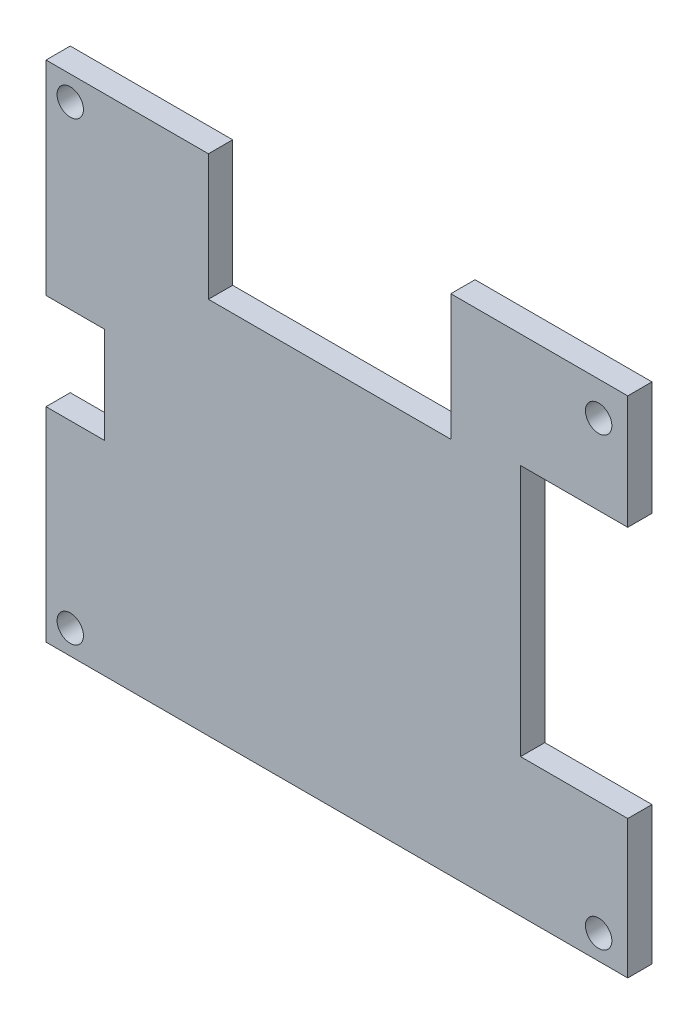
SolidWorks part; units mm, degrees
ref_plane "Front Plane" through (0, 0, 0) normal (0, 0, 1) x (1, 0, 0)
ref_plane "Top Plane" through (0, 0, 0) normal (0, 1, 0) x (1, 0, 0)
ref_plane "Right Plane" through (0, 0, 0) normal (1, 0, 0) x (0, 0, -1)
sketch "Sketch1" plane through (0, 0, 0) normal (0, 0, 1) x (1, 0, 0)
  line L0 (38.1, 1.5875) -> (24.0608, 1.5875) construction
  line L1 (-38.1, 33.02) -> (38.1, 33.02) construction
  line L2 (-38.1, 33.02) -> (-38.1, -33.02) construction
  line L3 (-38.1, -33.02) -> (38.1, -33.02) construction
  line L4 (38.1, 33.02) -> (38.1, -33.02) construction
  line L5 (-38.1, 33.02) -> (38.1, -33.02) construction
  line L6 (-38.1, -33.02) -> (38.1, 33.02) construction
  line L7 (-41.275, 6.3059) -> (-41.275, -6.3059)
  line L8 (-41.275, 6.3059) -> (-30.4454, 6.3059)
  line L9 (41.275, 18.1012) -> (41.275, -14.9262)
  line L10 (-41.275, -6.3059) -> (-30.4454, -6.3059)
  line L11 (-30.4454, 6.3059) -> (-30.4454, -6.3059)
  line L12 (41.275, 18.1012) -> (24.0608, 18.1012)
  line L13 (-34.925, 0) -> (-30.4454, 0) construction
  line L15 (41.275, -14.9262) -> (24.0608, -14.9262)
  line L16 (24.0608, 18.1012) -> (24.0608, -14.9262)
  line L18 (-16.8275, 16.51) -> (14.9225, 16.51)
  line L20 (-16.8275, 16.51) -> (-16.8275, 36.195)
  line L21 (-16.8275, 36.195) -> (14.9225, 36.195)
  line L22 (14.9225, 16.51) -> (14.9225, 36.195)
  point P0 (0, 0)
  point P6 (-34.925, 0)
  point P7 (33.655, 10.795)
  point P8 (-9.525, 20.32)
  point P9 (6.35, 24.13)
  point P10 (33.655, -7.62)
  point P11 (33.655, 1.5875)
  point P15 (33.655, 1.5875)
  point P29 (-16.8275, 16.51)
  point P30 (14.9225, 33.02)
  point P37 (-34.925, 29.845)
  point P38 (34.29, 28.575)
  point P40 (34.29, -29.845)
  point P42 (-34.925, -29.845)
  dimension "D1" = 76.2
  dimension "D2" = 66.04
  dimension "D3" = 3.175
  dimension "D4" = 33.02
  dimension "D5" = 28.575
  dimension "D6" = 53.34
  dimension "D7" = 57.15
  dimension "D8" = 44.45
  dimension "D9" = 71.755
  dimension "D10" = 43.815
  dimension "D11" = 25.4
  dimension "D12" = 71.755
  dimension "D13" = 71.755
  dimension "D14" = 34.6075
  dimension "D15" = 21.2725
  dimension "D16" = 49.53
  dimension "D17" = 53.0225
  dimension "D18" = 66.04
sketch "Sketch2" plane through (0, 0, 0) normal (0, 0, 1) x (1, 0, 0)
  line L0 (-38.1, 33.02) -> (-16.8275, 33.02)
  line L1 (-16.8275, 16.51) -> (-16.8275, 36.195) construction
  line L2 (-38.1, 33.02) -> (38.1, 33.02) construction
  line L3 (-16.8275, 33.02) -> (-16.8275, 16.51)
  line L4 (-16.8275, 16.51) -> (14.9225, 16.51)
  line L5 (14.9225, 16.51) -> (14.9225, 33.02)
  line L6 (14.9225, 33.02) -> (38.1, 33.02)
  line L7 (38.1, 33.02) -> (38.1, 18.1012)
  line L8 (41.275, 18.1012) -> (24.0608, 18.1012) construction
  line L9 (38.1, 33.02) -> (38.1, -33.02) construction
  line L10 (38.1, 18.1012) -> (24.0608, 18.1012)
  line L11 (24.0608, 18.1012) -> (24.0608, -14.9262)
  line L12 (24.0608, -14.9262) -> (38.1, -14.9262)
  line L13 (41.275, -14.9262) -> (24.0608, -14.9262) construction
  line L14 (38.1, -14.9262) -> (38.1, -33.02)
  line L15 (38.1, -33.02) -> (-38.1, -33.02)
  line L16 (-38.1, -33.02) -> (-38.1, -6.3059)
  line L17 (-41.275, -6.3059) -> (-30.4454, -6.3059) construction
  line L18 (-38.1, 33.02) -> (-38.1, -33.02) construction
  line L19 (-38.1, -6.3059) -> (-30.4454, -6.3059)
  line L20 (-30.4454, -6.3059) -> (-30.4454, 6.3059)
  line L21 (-30.4454, 6.3059) -> (-38.1, 6.3059)
  line L22 (-41.275, 6.3059) -> (-30.4454, 6.3059) construction
  line L23 (-38.1, 6.3059) -> (-38.1, 33.02)
extrude "Boss-Extrude1" add sketch "Sketch2" along normal blind 3.175
hole_wizard "#4 Clearance Hole1" positions "Sketch4" profile "Sketch3" hole size "#4" standard "ANSI Inch"
sketch "Sketch4" plane through (0, 0, 3.175) normal (0, 0, 1) x (1, 0, 0)
  point P0 (-34.925, 29.845)
  point P3 (34.29, 28.575)
  point P6 (-34.925, -29.845)
  point P9 (34.29, -29.845)
sketch "Sketch3" plane through (-34.925, 29.845, 3.175) normal (1, 0, 0) x (0, -1, 0)
  line L0 (0, 0) -> (0, 11.1978)
  line L1 (0, 11.1978) -> (1.7272, 10.16)
  line L2 (1.7272, 10.16) -> (1.7272, 0)
  line L5 (1.7272, 0) -> (0, 0)
  line L10 (0, 11.1978) -> (-1.7272, 10.16) construction
  line L11 (0, -6.35) -> (0, 107.95) construction
  dimension "Hole Dia." = 3.4544
  dimension "Hole Depth" = 10.16
  dimension "Drill Angle" = 118
